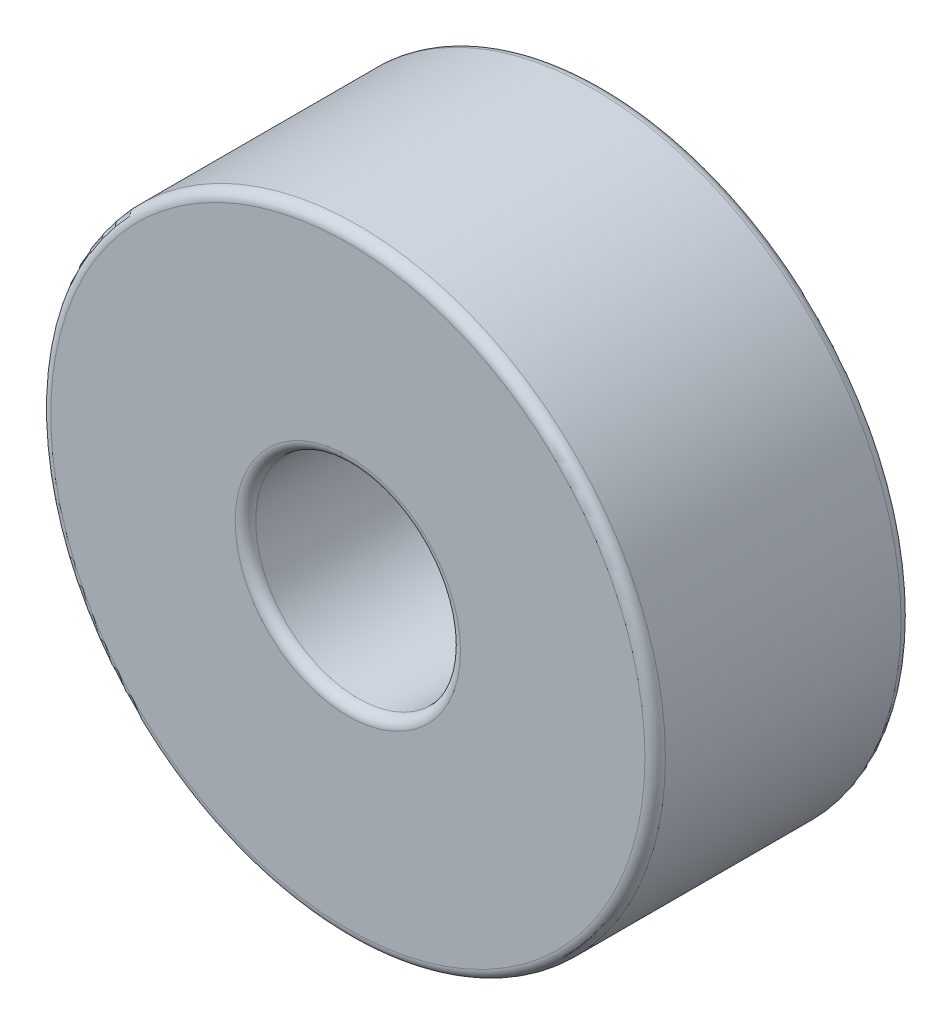
SolidWorks part; units mm, degrees
material "Brass"
ref_plane "Front Plane" through (0, 0, 0) normal (0, 0, 1) x (1, 0, 0)
ref_plane "Top Plane" through (0, 0, 0) normal (0, 1, 0) x (1, 0, 0)
ref_plane "Right Plane" through (0, 0, 0) normal (1, 0, 0) x (0, 0, -1)
sketch "Sketch1" plane through (0, 0, 0) normal (0, 0, 1) x (1, 0, 0)
  circle A0 centre (0, 0) radius 3
  circle A1 centre (0, 0) radius 1
  dimension "D1" = 6
  dimension "D2" = 2
extrude "Boss-Extrude1" add sketch "Sketch1" along normal blind 2.5
fillet "Fillet1" radius 0.1 1 edges at (3, 0, 2.5)
fillet "Fillet2" radius 0.1 3 edges at (1, 0, 0) (1, 0, 2.5) (3, 0, 0)
